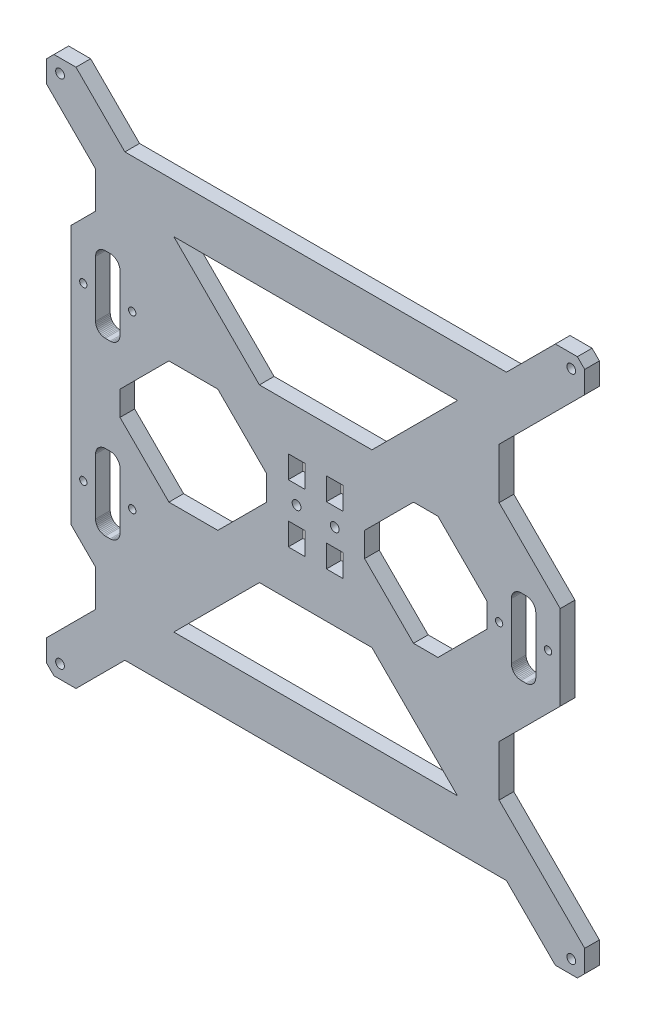
SolidWorks part; units mm, degrees
ref_plane "Plano frontal" through (0, 0, 0) normal (0, 0, 1) x (1, 0, 0)
ref_plane "Plano superior" through (0, 0, 0) normal (0, 1, 0) x (1, 0, 0)
ref_plane "Plano direito" through (0, 0, 0) normal (1, 0, 0) x (0, 0, -1)
sketch "Model" plane through (0, 0, 0) normal (0, 0, 1) x (1, 0, 0)
  line L0 (46.5061, 107.5061) -> (46.0368, 107.2747)
  line L1 (45.6018, 106.984) -> (45.2084, 106.639)
  line L2 (46.0368, 107.2747) -> (45.6018, 106.984)
  line L3 (36.0368, 16.8106) -> (56.0368, 36.8106)
  line L4 (34.0368, 73.8106) -> (44.0368, 63.8106)
  line L5 (44.0368, 189.8105) -> (34.0368, 179.8106)
  line L6 (24.0368, 28.8106) -> (24.0368, 19.8106)
  line L7 (52.8653, 77.9822) -> (53.2103, 78.3755)
  line L8 (51.5676, 107.5061) -> (51.0721, 107.6743)
  line L9 (51.0721, 107.6743) -> (50.5589, 107.7764)
  line L10 (50.5589, 107.7764) -> (50.0368, 107.8106)
  line L11 (24.0368, 19.8106) -> (27.0368, 16.8106)
  line L12 (54.0026, 80.2885) -> (54.0368, 80.8106)
  line L13 (50.5589, 76.8448) -> (51.0721, 76.9469)
  line L14 (46.5061, 77.1151) -> (47.0016, 76.9469)
  line L15 (46.0368, 77.3465) -> (46.5061, 77.1151)
  line L16 (244.0368, 224.8105) -> (209.0368, 189.8105)
  line L17 (52.0368, 107.2747) -> (51.5676, 107.5061)
  line L18 (44.3413, 105.3413) -> (44.1731, 104.8459)
  line L19 (44.1731, 104.8459) -> (44.0711, 104.3327)
  line L20 (44.0711, 104.3327) -> (44.0368, 103.8106)
  line L21 (48.0368, 107.8106) -> (50.0368, 107.8106)
  line L22 (232.0368, 16.8106) -> (212.0368, 36.8106)
  line L23 (36.0368, 236.8105) -> (56.0368, 216.8105)
  line L24 (45.6018, 77.6372) -> (46.0368, 77.3465)
  line L25 (45.2084, 77.9822) -> (45.6018, 77.6372)
  line L26 (50.0368, 76.8106) -> (48.0368, 76.8106)
  line L27 (48.0368, 107.8106) -> (47.5147, 107.7764)
  line L28 (47.5147, 107.7764) -> (47.0016, 107.6743)
  line L29 (44.0368, 80.8106) -> (44.0368, 103.8106)
  line L30 (44.0368, 80.8106) -> (44.0711, 80.2885)
  line L31 (44.0711, 80.2885) -> (44.1731, 79.7753)
  line L32 (24.0368, 224.8105) -> (44.0368, 204.8105)
  line L33 (53.9005, 104.8459) -> (53.7324, 105.3413)
  line L34 (54.0026, 104.3327) -> (53.9005, 104.8459)
  line L35 (54.0368, 103.8106) -> (54.0026, 104.3327)
  line L36 (27.0368, 236.8105) -> (24.0368, 233.8105)
  line L37 (241.0368, 236.8105) -> (232.0368, 236.8105)
  line L38 (53.7324, 105.3413) -> (53.5009, 105.8106)
  line L39 (53.5009, 105.8106) -> (53.2103, 106.2456)
  line L40 (244.0368, 28.8106) -> (244.0368, 19.8106)
  line L41 (44.0368, 48.8106) -> (44.0368, 63.8106)
  line L42 (44.3413, 79.2799) -> (44.5727, 78.8106)
  line L43 (44.5727, 78.8106) -> (44.8634, 78.3755)
  line L44 (53.2103, 106.2456) -> (52.8653, 106.639)
  line L45 (44.8634, 78.3755) -> (45.2084, 77.9822)
  line L46 (54.0368, 103.8106) -> (54.0368, 80.8106)
  line L47 (44.5727, 105.8106) -> (44.3413, 105.3413)
  line L48 (51.5676, 77.1151) -> (52.0368, 77.3465)
  line L49 (52.0368, 77.3465) -> (52.4719, 77.6372)
  line L50 (52.4719, 77.6372) -> (52.8653, 77.9822)
  line L51 (51.0721, 76.9469) -> (51.5676, 77.1151)
  line L52 (241.0368, 16.8106) -> (244.0368, 19.8106)
  line L53 (53.7324, 79.2799) -> (53.9005, 79.7753)
  line L54 (53.9005, 79.7753) -> (54.0026, 80.2885)
  line L55 (52.4719, 106.984) -> (52.0368, 107.2747)
  line L56 (52.8653, 106.639) -> (52.4719, 106.984)
  line L57 (232.0368, 236.8105) -> (212.0368, 216.8105)
  line L58 (24.0368, 28.8106) -> (44.0368, 48.8106)
  line L59 (44.0368, 204.8105) -> (44.0368, 189.8105)
  line L60 (47.0016, 107.6743) -> (46.5061, 107.5061)
  line L61 (244.0368, 233.8105) -> (241.0368, 236.8105)
  line L62 (34.0368, 179.8106) -> (34.0368, 73.8106)
  line L63 (50.0368, 76.8106) -> (50.5589, 76.8448)
  line L64 (47.0016, 76.9469) -> (47.5147, 76.8448)
  line L65 (44.8634, 106.2456) -> (44.5727, 105.8106)
  line L66 (45.2084, 106.639) -> (44.8634, 106.2456)
  line L67 (53.2103, 78.3755) -> (53.5009, 78.8106)
  line L68 (53.5009, 78.8106) -> (53.7324, 79.2799)
  line L69 (44.1731, 79.7753) -> (44.3413, 79.2799)
  line L70 (47.5147, 76.8448) -> (48.0368, 76.8106)
  line L71 (56.0368, 216.8105) -> (212.0368, 216.8105)
  line L72 (209.0368, 63.8106) -> (209.0368, 84.5367)
  line L73 (56.0368, 36.8106) -> (212.0368, 36.8106)
  line L74 (209.0368, 169.1138) -> (209.0368, 189.8105)
  line L75 (216.5061, 141.369) -> (216.0368, 141.1375)
  line L76 (53.9005, 174.8529) -> (53.7324, 175.3483)
  line L77 (53.7324, 175.3483) -> (53.5009, 175.8176)
  line L78 (216.0368, 141.1375) -> (215.6017, 140.8469)
  line L79 (53.2103, 176.2526) -> (52.8653, 176.646)
  line L80 (217.0015, 141.5371) -> (216.5061, 141.369)
  line L81 (217.5147, 141.6392) -> (217.0015, 141.5371)
  line L82 (218.0368, 141.6734) -> (217.5147, 141.6392)
  line L83 (218.0368, 141.6734) -> (220.0368, 141.6734)
  line L84 (220.5589, 141.6392) -> (220.0368, 141.6734)
  line L85 (221.0721, 141.5371) -> (220.5589, 141.6392)
  line L86 (221.5675, 141.369) -> (221.0721, 141.5371)
  line L87 (222.0368, 141.1375) -> (221.5675, 141.369)
  line L88 (222.4718, 140.8469) -> (222.0368, 141.1375)
  line L89 (222.8652, 140.5019) -> (222.4718, 140.8469)
  line L90 (223.2102, 140.1085) -> (222.8652, 140.5019)
  line L91 (223.5009, 139.6734) -> (223.2102, 140.1085)
  line L92 (223.7323, 139.2042) -> (223.5009, 139.6734)
  line L93 (223.9005, 138.7087) -> (223.7323, 139.2042)
  line L94 (224.0026, 138.1955) -> (223.9005, 138.7087)
  line L95 (224.0368, 137.6734) -> (224.0026, 138.1955)
  line L96 (224.0368, 137.6734) -> (224.0368, 114.6734)
  line L97 (224.0026, 114.1513) -> (224.0368, 114.6734)
  line L98 (223.9005, 113.6382) -> (224.0026, 114.1513)
  line L99 (223.7323, 113.1427) -> (223.9005, 113.6382)
  line L100 (223.5009, 112.6734) -> (223.7323, 113.1427)
  line L101 (223.2102, 112.2384) -> (223.5009, 112.6734)
  line L102 (222.8652, 111.845) -> (223.2102, 112.2384)
  line L103 (222.4718, 111.5) -> (222.8652, 111.845)
  line L104 (222.0368, 111.2093) -> (222.4718, 111.5)
  line L105 (221.5675, 110.9779) -> (222.0368, 111.2093)
  line L106 (221.0721, 110.8097) -> (221.5675, 110.9779)
  line L107 (220.5589, 110.7077) -> (221.0721, 110.8097)
  line L108 (220.0368, 110.6735) -> (220.5589, 110.7077)
  line L109 (220.0368, 110.6735) -> (218.0368, 110.6735)
  line L110 (217.5147, 110.7077) -> (218.0368, 110.6735)
  line L111 (217.0015, 110.8097) -> (217.5147, 110.7077)
  line L112 (216.5061, 110.9779) -> (217.0015, 110.8097)
  line L113 (216.0368, 111.2093) -> (216.5061, 110.9779)
  line L114 (215.6017, 111.5) -> (216.0368, 111.2093)
  line L115 (215.2084, 111.845) -> (215.6017, 111.5)
  line L116 (214.8634, 112.2384) -> (215.2084, 111.845)
  line L117 (214.5727, 112.6734) -> (214.8634, 112.2384)
  line L118 (214.3413, 113.1427) -> (214.5727, 112.6734)
  line L119 (214.1731, 113.6382) -> (214.3413, 113.1427)
  line L120 (214.071, 114.1513) -> (214.1731, 113.6382)
  line L121 (214.0368, 114.6734) -> (214.071, 114.1513)
  line L122 (214.0368, 114.6734) -> (214.0368, 137.6734)
  line L123 (214.071, 138.1955) -> (214.0368, 137.6734)
  line L124 (214.1731, 138.7087) -> (214.071, 138.1955)
  line L125 (214.3413, 139.2042) -> (214.1731, 138.7087)
  line L126 (214.5727, 139.6734) -> (214.3413, 139.2042)
  line L127 (214.8634, 140.1085) -> (214.5727, 139.6734)
  line L128 (215.2084, 140.5019) -> (214.8634, 140.1085)
  line L129 (215.6017, 140.8469) -> (215.2084, 140.5019)
  line L130 (54.0026, 174.3397) -> (53.9005, 174.8529)
  line L131 (54.0368, 173.8176) -> (54.0026, 174.3397)
  line L132 (54.0368, 173.8176) -> (54.0368, 150.8176)
  line L133 (54.0026, 150.2955) -> (54.0368, 150.8176)
  line L134 (53.9005, 149.7823) -> (54.0026, 150.2955)
  line L135 (53.7324, 149.2869) -> (53.9005, 149.7823)
  line L136 (53.5009, 148.8176) -> (53.7324, 149.2869)
  line L137 (53.2103, 148.3826) -> (53.5009, 148.8176)
  line L138 (52.8653, 147.9892) -> (53.2103, 148.3826)
  line L139 (52.4719, 147.6442) -> (52.8653, 147.9892)
  line L140 (52.0368, 147.3535) -> (52.4719, 147.6442)
  line L141 (51.5676, 147.1221) -> (52.0368, 147.3535)
  line L142 (51.0721, 146.9539) -> (51.5676, 147.1221)
  line L143 (50.5589, 146.8518) -> (51.0721, 146.9539)
  line L144 (50.0368, 146.8176) -> (50.5589, 146.8518)
  line L145 (50.0368, 146.8176) -> (48.0368, 146.8176)
  line L146 (47.5147, 146.8518) -> (48.0368, 146.8176)
  line L147 (47.0016, 146.9539) -> (47.5147, 146.8518)
  line L148 (46.5061, 147.1221) -> (47.0016, 146.9539)
  line L149 (46.0368, 147.3535) -> (46.5061, 147.1221)
  line L150 (45.6018, 147.6442) -> (46.0368, 147.3535)
  line L151 (45.2084, 147.9892) -> (45.6018, 147.6442)
  line L152 (44.8634, 148.3826) -> (45.2084, 147.9892)
  line L153 (44.5727, 148.8176) -> (44.8634, 148.3826)
  line L154 (44.3413, 149.2869) -> (44.5727, 148.8176)
  line L155 (44.1731, 149.7823) -> (44.3413, 149.2869)
  line L156 (44.0711, 150.2955) -> (44.1731, 149.7823)
  line L157 (44.0368, 150.8176) -> (44.0711, 150.2955)
  line L158 (44.0368, 150.8176) -> (44.0368, 173.8176)
  line L159 (44.0711, 174.3397) -> (44.0368, 173.8176)
  line L160 (44.1731, 174.8529) -> (44.0711, 174.3397)
  line L161 (44.3413, 175.3483) -> (44.1731, 174.8529)
  line L162 (44.5727, 175.8176) -> (44.3413, 175.3483)
  line L163 (44.8634, 176.2526) -> (44.5727, 175.8176)
  line L164 (45.2084, 176.646) -> (44.8634, 176.2526)
  line L165 (45.6018, 176.991) -> (45.2084, 176.646)
  line L166 (46.0368, 177.2817) -> (45.6018, 176.991)
  line L167 (46.5061, 177.5131) -> (46.0368, 177.2817)
  line L168 (47.0016, 177.6813) -> (46.5061, 177.5131)
  line L169 (47.5147, 177.7834) -> (47.0016, 177.6813)
  line L170 (48.0368, 177.8176) -> (47.5147, 177.7834)
  line L171 (48.0368, 177.8176) -> (50.0368, 177.8176)
  line L172 (50.5589, 177.7834) -> (50.0368, 177.8176)
  line L173 (51.0721, 177.6813) -> (50.5589, 177.7834)
  line L174 (51.5676, 177.5131) -> (51.0721, 177.6813)
  line L175 (52.0368, 177.2817) -> (51.5676, 177.5131)
  line L176 (52.4719, 176.991) -> (52.0368, 177.2817)
  line L177 (52.8653, 176.646) -> (52.4719, 176.991)
  line L178 (53.5009, 175.8176) -> (53.2103, 176.2526)
  line L179 (76.0368, 196.8105) -> (192.0368, 196.8105)
  line L180 (192.0368, 196.8105) -> (157.0368, 161.8106)
  line L181 (157.0368, 161.8106) -> (111.0368, 161.8106)
  line L182 (76.0368, 196.8105) -> (111.0368, 161.8106)
  line L183 (114.0368, 131.8106) -> (114.0368, 121.8106)
  line L184 (114.0368, 121.8106) -> (94.0368, 101.8106)
  line L185 (94.0368, 101.8106) -> (74.0368, 101.8106)
  line L186 (74.0368, 101.8106) -> (54.0368, 121.8106)
  line L187 (54.0368, 121.8106) -> (54.0368, 131.8106)
  line L188 (54.0368, 131.8106) -> (74.0368, 151.8106)
  line L189 (74.0368, 151.8106) -> (94.0368, 151.8106)
  line L190 (94.0368, 151.8106) -> (114.0368, 131.8106)
  line L191 (204.0368, 131.8106) -> (204.0368, 121.8106)
  line L192 (184.0368, 101.8106) -> (174.0368, 101.8106)
  line L193 (174.0368, 101.8106) -> (154.0368, 121.8106)
  line L194 (154.0368, 121.8106) -> (154.0368, 131.8106)
  line L195 (154.0368, 131.8106) -> (174.0368, 151.8106)
  line L196 (174.0368, 151.8106) -> (184.0368, 151.8106)
  line L197 (111.0368, 91.8106) -> (76.0368, 56.8106)
  line L198 (157.0368, 91.8106) -> (111.0368, 91.8106)
  line L199 (192.0368, 56.8106) -> (157.0368, 91.8106)
  line L200 (76.0368, 56.8106) -> (192.0368, 56.8106)
  line L201 (122.835, 119.5442) -> (122.835, 110.3442)
  line L202 (122.835, 143.3441) -> (122.835, 134.1442)
  line L203 (129.635, 110.3442) -> (129.635, 119.5442)
  line L204 (129.635, 119.5442) -> (122.835, 119.5442)
  line L205 (129.635, 143.3441) -> (122.835, 143.3441)
  line L206 (122.835, 134.1442) -> (129.635, 134.1442)
  line L207 (129.635, 134.1442) -> (129.635, 143.3441)
  line L208 (122.835, 110.3442) -> (129.635, 110.3442)
  line L209 (24.0368, 233.8105) -> (24.0368, 224.8105)
  line L210 (209.0368, 63.8106) -> (244.0368, 28.8106)
  line L211 (244.0368, 233.8105) -> (244.0368, 224.8105)
  line L212 (36.0368, 236.8105) -> (27.0368, 236.8105)
  line L213 (241.0368, 16.8106) -> (232.0368, 16.8106)
  line L214 (27.0368, 16.8106) -> (36.0368, 16.8106)
  line L215 (234.0368, 144.1138) -> (209.0368, 169.1138)
  line L216 (234.0368, 109.5367) -> (209.0368, 84.5367)
  line L217 (204.0368, 121.8106) -> (184.0368, 101.8106)
  line L218 (184.0368, 151.8106) -> (204.0368, 131.8106)
  line L219 (194.1071, 111.8809) -> (194.1071, 111.8106)
  line L220 (94.0368, 151.8106) -> (94.1072, 151.8106)
  line L221 (194.1071, 141.8106) -> (194.1071, 141.7402)
  line L222 (234.0368, 144.1138) -> (234.0368, 109.5367)
  line L223 (145.2387, 119.5442) -> (145.2387, 110.3442)
  line L224 (145.2387, 143.3441) -> (145.2387, 134.1442)
  line L225 (138.4387, 110.3442) -> (138.4387, 119.5442)
  line L226 (138.4387, 119.5442) -> (145.2387, 119.5442)
  line L227 (138.4387, 143.3441) -> (145.2387, 143.3441)
  line L228 (145.2387, 134.1442) -> (138.4387, 134.1442)
  line L229 (138.4387, 134.1442) -> (138.4387, 143.3441)
  line L230 (145.2387, 110.3442) -> (138.4387, 110.3442)
  circle A0 centre (126.2332, 126.8444) radius 1.8
  circle A1 centre (29.5265, 231.3209) radius 1.8
  circle A2 centre (39.0368, 161.8106) radius 1.5
  circle A3 centre (59.0368, 161.8106) radius 1.5
  circle A4 centre (29.5265, 22.3002) radius 1.8
  circle A5 centre (39.0368, 91.8106) radius 1.5
  circle A6 centre (59.0368, 91.8106) radius 1.5
  circle A7 centre (238.5472, 231.3209) radius 1.8
  circle A8 centre (238.5472, 22.3002) radius 1.8
  circle A9 centre (209.0368, 126.8106) radius 1.5
  circle A10 centre (229.0368, 126.8106) radius 1.5
  circle A11 centre (141.8404, 126.8444) radius 1.8
extrude "Ressalto-extrusão1" add sketch "Model" along normal blind 6 contours L222 L215 L74 L16 L211 L61 L37 L57 L71 L23 L212 L36 L209 L32 L59 L5 L62 L4 L41 L58 L6 L11 L214 L3 L73 L22 L213 L52 L40 L210 L72 L216 A11 A10 A9 A8 A7 A6 A5 A4 A3
ref_plane "Plano1" through (219.0368, 0, 0) normal (-1, 0, 0) x (0, 0, 1)
ref_plane "Plano2" through (0, 126.1734, 0) normal (0, -1, 0) x (-1, 0, 0)
ref_plane "Plano3" through (49.0368, 0, 0) normal (-1, 0, 0) x (0, 0, 1)
ref_plane "Plano4" through (0, 92.3106, 0) normal (0, 1, 0) x (1, 0, 0)
ref_plane "Plano5" through (0, 162.3176, 0) normal (0, -1, 0) x (-1, 0, 0)
